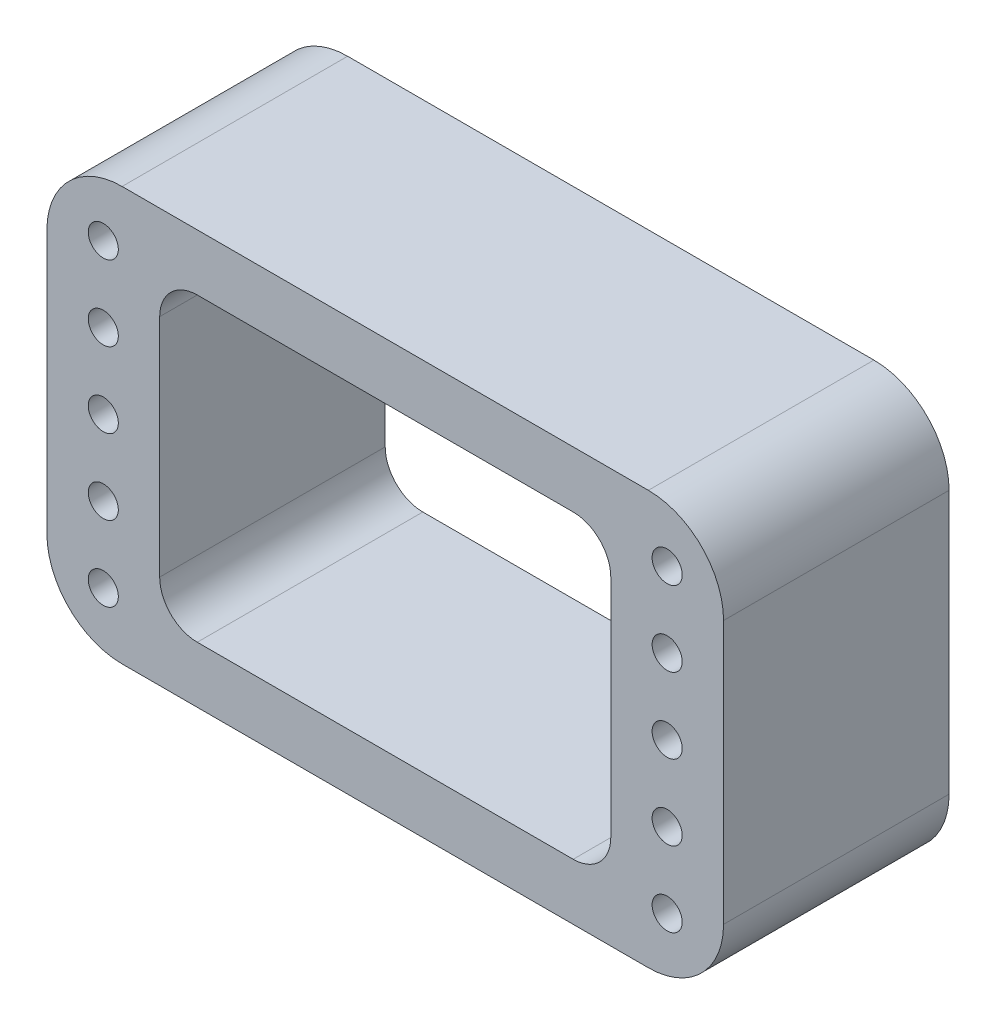
SolidWorks part; units mm, degrees
ref_plane "Front Plane" through (0, 0, 0) normal (0, 0, 1) x (1, 0, 0)
ref_plane "Top Plane" through (0, 0, 0) normal (0, 1, 0) x (1, 0, 0)
ref_plane "Right Plane" through (0, 0, 0) normal (1, 0, 0) x (0, 0, -1)
sketch "Sketch1" plane through (0, 0, 0) normal (0, 0, 1) x (1, 0, 0)
  line L1 (-45, 27.5) -> (45, 27.5)
  line L2 (-45, 27.5) -> (-45, -27.5)
  line L3 (-45, -27.5) -> (45, -27.5)
  line L4 (45, 27.5) -> (45, -27.5)
  line L5 (-45, 27.5) -> (45, -27.5) construction
  line L6 (-45, -27.5) -> (45, 27.5) construction
  point P0 (0, 0)
  dimension "D1" = 90
  dimension "D2" = 55
extrude "Boss-Extrude1" add sketch "Sketch1" along normal blind 30
sketch "Sketch2" plane through (0, 0, 30) normal (0, 0, 1) x (1, 0, 0)
  line L1 (-30, 20) -> (30, 20)
  line L2 (-30, 20) -> (-30, -20)
  line L3 (-30, -20) -> (30, -20)
  line L4 (30, 20) -> (30, -20)
  line L5 (-30, 20) -> (30, -20) construction
  line L6 (-30, -20) -> (30, 20) construction
  point P0 (0, 0)
  dimension "D1" = 60
  dimension "D2" = 40
extrude "Cut-Extrude1" cut sketch "Sketch2" against normal through all
sketch "Sketch3" plane through (0, 0, 0) normal (0, 0, -1) x (-1, 0, 0)
  line L0 (-37.5, 0) -> (37.5, 0) construction
  circle A0 centre (-37.5, 0) radius 2
  circle A1 centre (37.5, 0) radius 2
  point P3 (0, 0)
  dimension "D2" = 4
  dimension "D3" = 4
  dimension "D1" = 75
extrude "Cut-Extrude2" cut sketch "Sketch3" against normal through all
pattern_linear "LPattern1" count 3 spacing 10 along (0, -1, 0) count 3 spacing 10 along (0, 1, 0) of "Cut-Extrude2"
fillet "Fillet1" radius 10 4 edges at (-45, 27.5, 15) (-45, -27.5, 15) (45, 27.5, 15) (45, -27.5, 15)
fillet "Fillet2" radius 5 4 edges at (-30, -20, 15) (30, -20, 15) (30, 20, 15) (-30, 20, 15)
